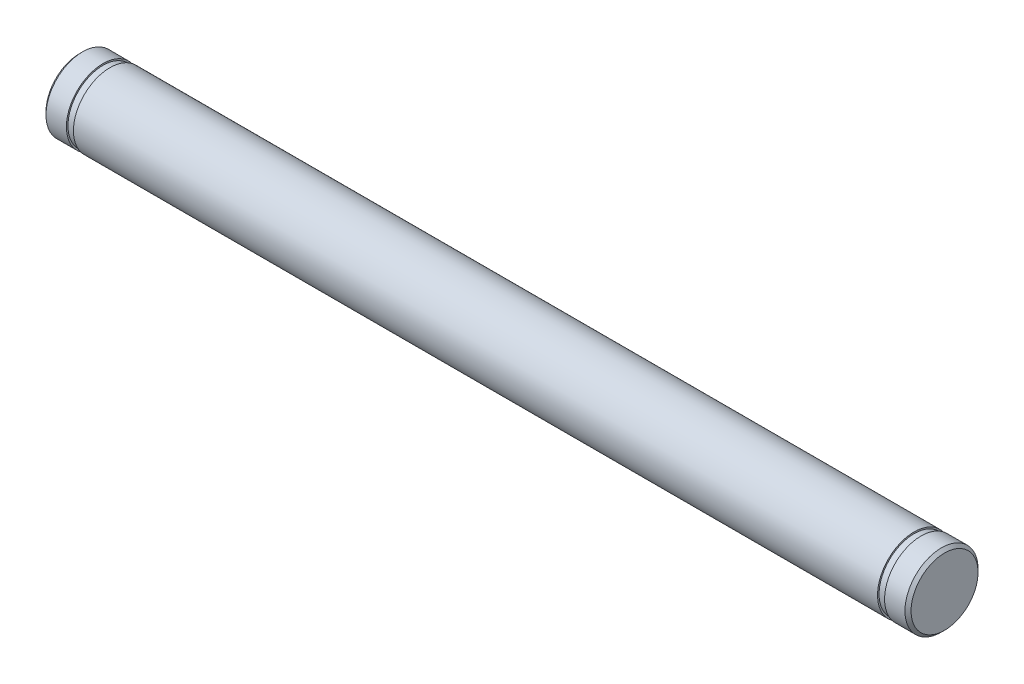
SolidWorks part; units mm, degrees
ref_plane "正面" through (0, 0, 0) normal (0, 0, 1) x (1, 0, 0)
ref_plane "平面" through (0, 0, 0) normal (0, 1, 0) x (1, 0, 0)
ref_plane "右側面" through (0, 0, 0) normal (1, 0, 0) x (0, 0, -1)
ref_plane "平面1" through (0, 0, 0) normal (0, 0, 1) x (1, 0, 0)
sketch "ｽｹｯﾁ1" plane through (0, 0, 0) normal (0, 0, 1) x (1, 0, 0)
  line L0 (0, 0) -> (0, 5.5)
  line L1 (0, 5.5) -> (0.5, 6)
  line L2 (0.5, 6) -> (141.5, 6)
  line L3 (141.5, 6) -> (142, 5.5)
  line L4 (142, 5.5) -> (142, 0)
  line L5 (142, 0) -> (0, 0)
  line L6 (142, 0) -> (0, 0) construction
revolve "回転1" add sketch "ｽｹｯﾁ1" angle 360 about L6
ref_plane "平面2" through (5, 0, 0) normal (1, 0, 0) x (0, 0, -1)
sketch "ｽｹｯﾁ2" plane through (5, 0, 0) normal (1, 0, 0) x (0, 0, -1)
  circle A0 centre (0, 0) radius 12
  circle A1 centre (0, 0) radius 5.75
extrude "ｶｯﾄ - 押し出し1" cut sketch "ｽｹｯﾁ2" against normal blind 1.15
ref_plane "平面3" through (137, 0, 0) normal (1, 0, 0) x (0, 0, -1)
sketch "ｽｹｯﾁ3" plane through (137, 0, 0) normal (1, 0, 0) x (0, 0, -1)
  circle A0 centre (0, 0) radius 12
  circle A1 centre (0, 0) radius 5.75
extrude "ｶｯﾄ - 押し出し2" cut sketch "ｽｹｯﾁ3" along normal blind 1.15
